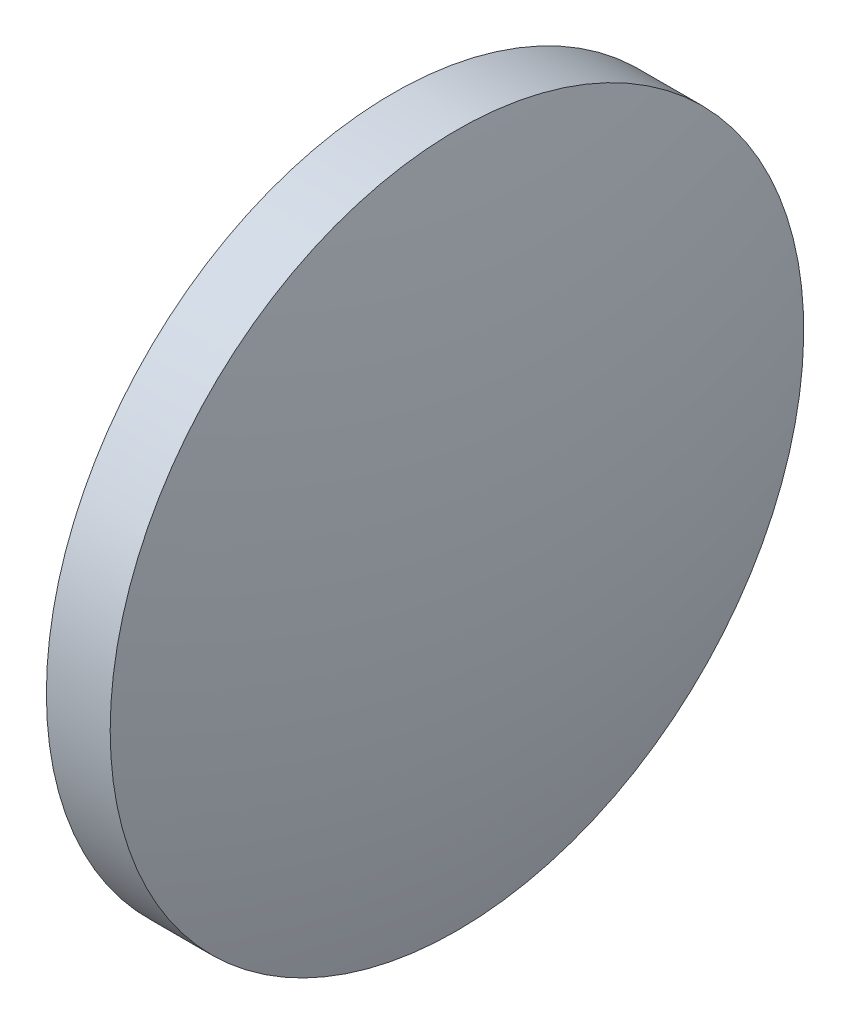
SolidWorks part; units mm, degrees
ref_plane "前视基准面" through (0, 0, 0) normal (0, 0, 1) x (1, 0, 0)
ref_plane "上视基准面" through (0, 0, 0) normal (0, 1, 0) x (1, 0, 0)
ref_plane "右视基准面" through (0, 0, 0) normal (1, 0, 0) x (0, 0, -1)
sketch "草图1" plane through (0, 0, 0) normal (0, 0, 1) x (1, 0, 0)
  line L0 (576.6615, 147.2766) -> (586.9957, 147.2766) construction
  line L1 (578.9882, 147.2766) -> (578.9882, 154.7766)
  line L2 (581.2882, 147.2766) -> (578.9882, 147.2766)
  line L3 (578.9882, 154.7766) -> (580.3682, 154.7766)
  arc A0 (581.2882, 147.2766) -> (580.3682, 154.7766) centre (550.2575, 147.2766) ccw
revolve "旋转1" add sketch "草图1" angle 360 about L0
